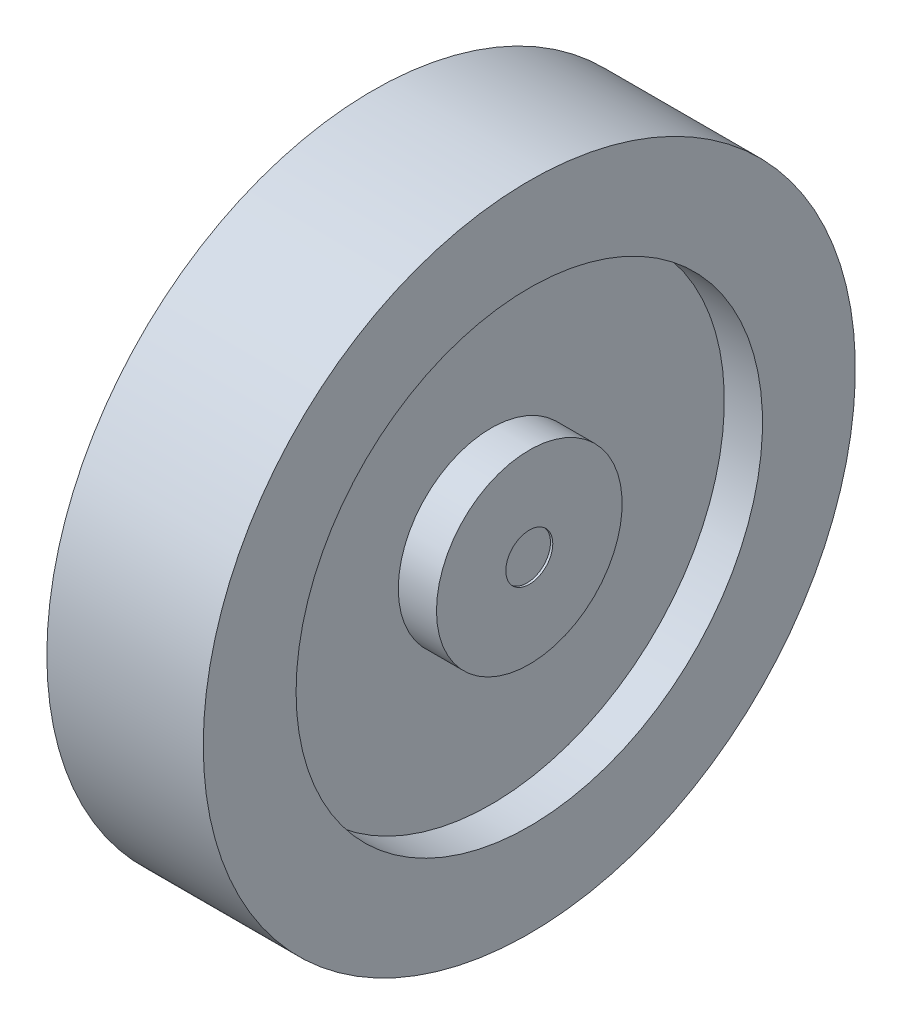
SolidWorks part; units mm, degrees
ref_plane "Front Plane" through (0, 0, 0) normal (0, 0, 1) x (1, 0, 0)
ref_plane "Top Plane" through (0, 0, 0) normal (0, 1, 0) x (1, 0, 0)
ref_plane "Right Plane" through (0, 0, 0) normal (1, 0, 0) x (0, 0, -1)
sketch "Sketch1" plane through (0, 0, 0) normal (0, 0, 1) x (1, 0, 0)
  line L0 (0, 0) -> (0, 35.687)
  line L1 (8.5601, 35.687) -> (-8.5601, 35.687)
  line L2 (-8.5601, 35.687) -> (-8.5601, 25.527)
  line L3 (-8.5601, 25.527) -> (-4.3796, 25.527)
  line L4 (-4.3796, 25.527) -> (-4.3796, 10.16)
  line L5 (-4.3796, 10.16) -> (-8.5601, 10.16)
  line L6 (-8.5601, 10.16) -> (-8.5601, 0)
  line L7 (-8.5601, 0) -> (-0.4977, 0)
  line L8 (8.5601, 0) -> (0.4977, 0)
  line L9 (8.5601, 10.16) -> (8.5601, 0)
  line L10 (4.3796, 10.16) -> (8.5601, 10.16)
  line L11 (4.3796, 25.527) -> (4.3796, 10.16)
  line L12 (8.5601, 25.527) -> (4.3796, 25.527)
  line L13 (8.5601, 35.687) -> (8.5601, 25.527)
  dimension "D1" = 35.687
  dimension "D2" = 10.16
  dimension "0.4" = 10.16
revolve "Revolve-Thin3" add sketch "Sketch1" angle 360 about L7
sketch "Sketch2" plane through (-8.5601, 0, 0) normal (-1, 0, 0) x (0, 0, 1)
  circle A0 centre (0, 0) radius 2.5711
extrude "Cut-Extrude2" cut sketch "Sketch2" against normal blind 25.4
